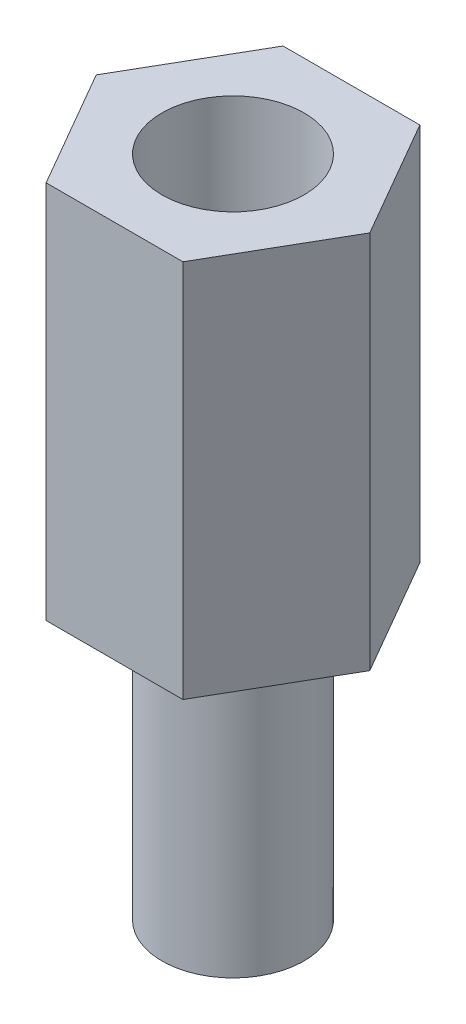
SolidWorks part; units mm, degrees
material "ABS"
ref_plane "Alzado" through (0, 0, 0) normal (0, 0, 1) x (1, 0, 0)
ref_plane "Planta" through (0, 0, 0) normal (0, 1, 0) x (1, 0, 0)
ref_plane "Vista lateral" through (0, 0, 0) normal (1, 0, 0) x (0, 0, -1)
sketch "Croquis1" plane through (0, 0, 0) normal (0, 1, 0) x (1, 0, 0)
  line L1 (1.4434, -2.5) -> (2.8868, 0)
  line L2 (2.8868, 0) -> (1.4434, 2.5)
  line L3 (1.4434, 2.5) -> (-1.4434, 2.5)
  line L4 (-1.4434, 2.5) -> (-2.8868, 0)
  line L5 (-2.8868, 0) -> (-1.4434, -2.5)
  line L6 (-1.4434, -2.5) -> (1.4434, -2.5)
  circle A0 centre (0, 0) radius 2.5 construction
  circle A1 centre (0, 0) radius 1.5
  dimension "D2" = 3
  dimension "D1" = 5
extrude "Saliente-Extruir1" add sketch "Croquis1" along normal blind 8
sketch "Croquis2" plane through (0, 0, 0) normal (0, -1, 0) x (1, 0, 0)
  circle A0 centre (0, 0) radius 1.5 construction
  circle A1 centre (0, 0) radius 1.5
extrude "Saliente-Extruir2" add sketch "Croquis2" along normal blind 6 separate body
